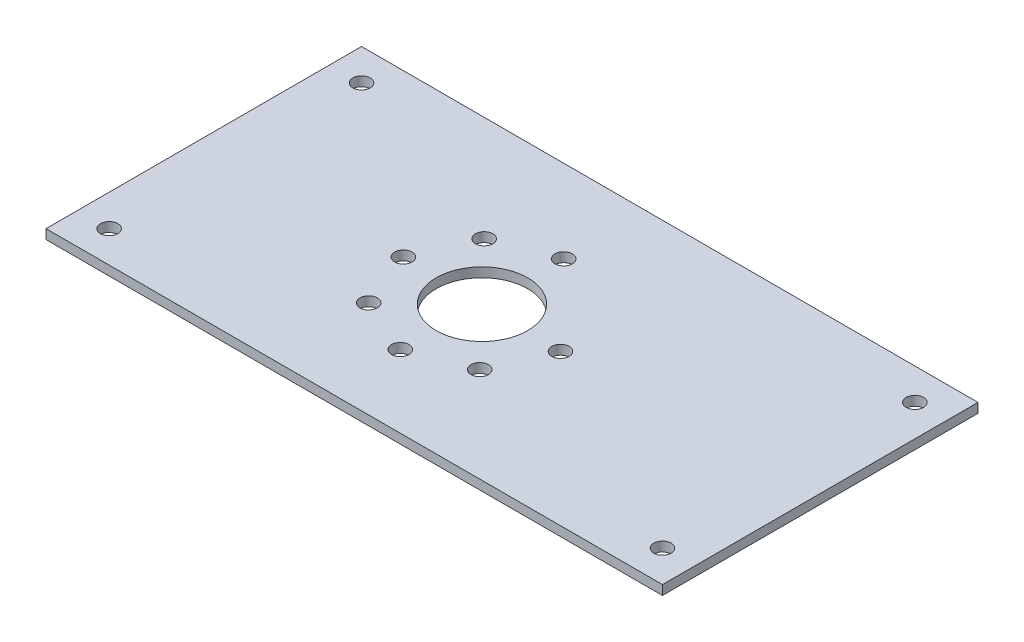
SolidWorks part; units mm, degrees
ref_plane "Front Plane" through (0, 0, 0) normal (0, 0, 1) x (1, 0, 0)
ref_plane "Top Plane" through (0, 0, 0) normal (0, 1, 0) x (1, 0, 0)
ref_plane "Right Plane" through (0, 0, 0) normal (1, 0, 0) x (0, 0, -1)
sketch "Sketch1" plane through (0, 0, 0) normal (0, 1, 0) x (1, 0, 0)
  line L1 (0, 0) -> (195.38, 0)
  line L2 (0, 0) -> (0, -100)
  line L3 (0, -100) -> (195.38, -100)
  line L4 (195.38, 0) -> (195.38, -100)
  dimension "D1" = 195.38
  dimension "D2" = 100
extrude "Boss-Extrude1" add sketch "Sketch1" along normal blind 3
sketch "Sketch2" plane through (0, 3, 0) normal (0, 1, 0) x (1, 0, 0)
  line L0 (195.38, 0) -> (0, 0) construction
  line L1 (195.38, -100) -> (195.38, 0) construction
  line L2 (0, -100) -> (195.38, -100) construction
  line L3 (0, 0) -> (0, -100) construction
  circle A2 centre (185.38, -10) radius 2.75
  circle A3 centre (185.38, -90) radius 2.75
  circle A4 centre (10, -90) radius 2.75
  circle A5 centre (10, -10) radius 2.75
  dimension "D1" = 5.5
  dimension "D2" = 10
  dimension "D3" = 5.5
  dimension "D4" = 5.5
  dimension "D5" = 5.5
  dimension "D6" = 10
  dimension "D7" = 10
  dimension "D8" = 10
extrude "Cut-Extrude1" cut sketch "Sketch2" against normal through all
sketch "Sketch3" plane through (0, 3, 0) normal (0, 1, 0) x (1, 0, 0)
  circle A21 centre (71.5021, -69.2529) radius 2.0193 construction
  circle A22 centre (64.4194, -51.1488) radius 2.0193 construction
  circle A23 centre (89.312, -77.0463) radius 2.0193 construction
  circle A24 centre (107.4161, -69.9635) radius 2.0193 construction
  circle A25 centre (115.2095, -52.1537) radius 2.0193 construction
  circle A26 centre (90.3169, -26.2562) radius 2.0193 construction
  circle A27 centre (72.2127, -33.339) radius 2.0193 construction
  circle A28 centre (71.5021, -69.2529) radius 2.0193 construction
  circle A29 centre (64.4194, -51.1488) radius 2.0193 construction
  circle A30 centre (89.312, -77.0463) radius 2.0193 construction
  circle A31 centre (107.4161, -69.9635) radius 2.0193 construction
  circle A32 centre (115.2095, -52.1537) radius 2.0193 construction
  circle A33 centre (90.3169, -26.2562) radius 2.0193 construction
  circle A34 centre (72.2127, -33.339) radius 2.0193 construction
  circle A35 centre (90.3169, -26.2562) radius 2.75
  circle A36 centre (72.2127, -33.339) radius 2.75
  circle A37 centre (64.4194, -51.1488) radius 2.75
  circle A38 centre (115.2095, -52.1537) radius 2.75
  circle A39 centre (107.4161, -69.9635) radius 2.75
  circle A40 centre (89.312, -77.0463) radius 2.75
  circle A41 centre (71.5021, -69.2529) radius 2.75
  circle A42 centre (89.8144, -51.6512) radius 9.525 construction
  circle A43 centre (89.8144, -51.6512) radius 9.525 construction
  circle A44 centre (89.8144, -51.6512) radius 14.5
  dimension "D1" = 5.5
  dimension "D2" = 5.5
  dimension "D3" = 5.5
  dimension "D4" = 5.5
  dimension "D5" = 5.5
  dimension "D6" = 5.5
  dimension "D7" = 5.5
  dimension "D8" = 29
extrude "Cut-Extrude2" cut sketch "Sketch3" against normal through all
